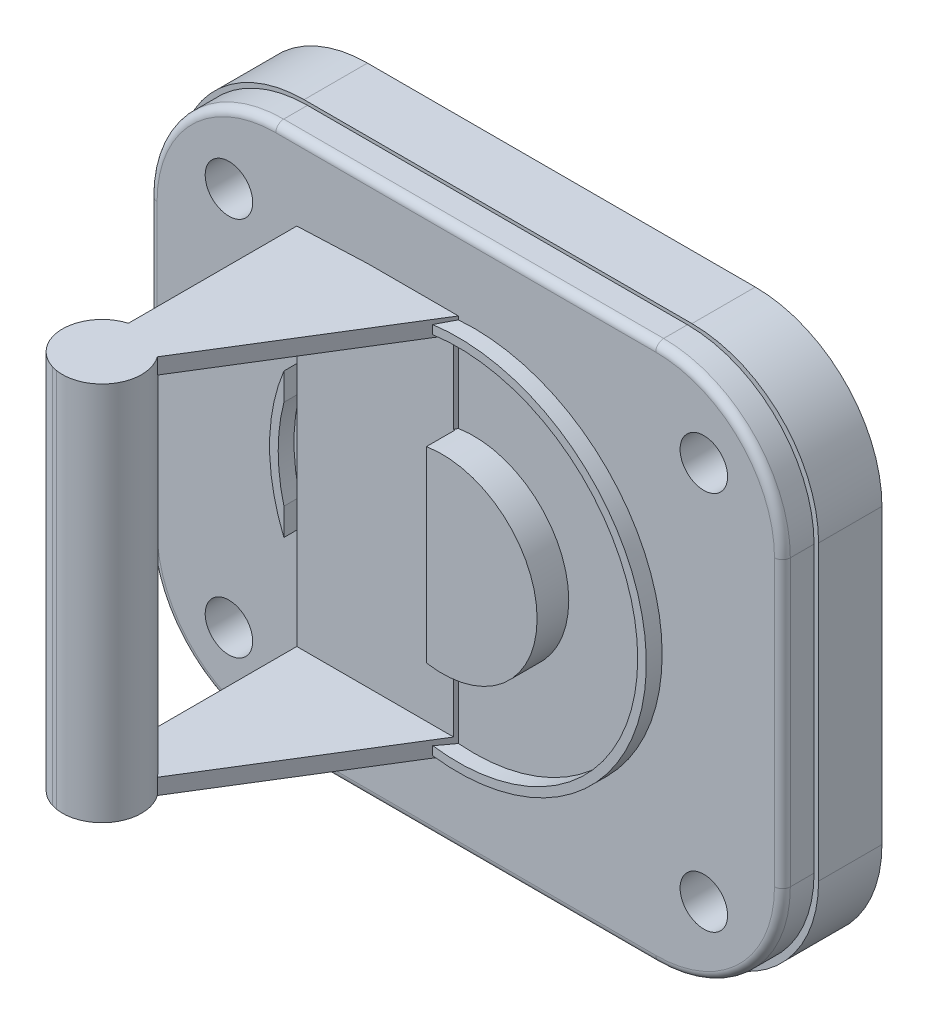
SolidWorks part; units mm, degrees
ref_plane "Front Plane" through (0, 0, 0) normal (0, 0, 1) x (1, 0, 0)
ref_plane "Top Plane" through (0, 0, 0) normal (0, 1, 0) x (1, 0, 0)
ref_plane "Right Plane" through (0, 0, 0) normal (1, 0, 0) x (0, 0, -1)
sketch "Sketch3" plane through (0, 0, 0) normal (0, 0, 1) x (1, 0, 0)
  line L5 (52.0332, 126.753) -> (82.0332, 102.753) construction
  line L6 (52.0332, 102.753) -> (82.0332, 126.753) construction
  line L7 (47.0332, 97.753) -> (87.0332, 97.753)
  line L8 (47.0332, 97.753) -> (47.0332, 131.753)
  line L9 (47.0332, 131.753) -> (87.0332, 131.753)
  line L10 (87.0332, 97.753) -> (87.0332, 131.753)
  line L11 (47.0332, 97.753) -> (87.0332, 131.753) construction
  line L12 (47.0332, 131.753) -> (87.0332, 97.753) construction
  circle A0 centre (82.0332, 126.753) radius 0.25
  circle A1 centre (52.0332, 126.753) radius 0.5
  circle A2 centre (52.0332, 102.753) radius 0.25
  circle A3 centre (82.0332, 102.753) radius 0.5
  circle A4 centre (55.0332, 129.753) radius 0.25 [skipped]
  circle A5 centre (79.0332, 99.753) radius 0.25 [skipped]
  point P0 (67.0332, 114.753)
  point P8 (67.0332, 114.753)
  point P15 (67.0332, 114.753)
  dimension "D3" = 0.5
  dimension "D5" = 1
  dimension "D6" = 1
  dimension "D1" = 30
  dimension "D2" = 24
  dimension "D7" = 40
  dimension "D8" = 34
  dimension "D4" = 4
extrude "Boss-Extrude2" add sketch "Sketch3" along normal blind 2
sketch "Sketch4" plane through (0, 0, 2) normal (0, 0, 1) x (1, 0, 0)
  circle A0 centre (67.5372, 114.9233) radius 6
  dimension "D1" = 12
extrude "Boss-Extrude3" add sketch "Sketch4" along normal blind 2
sketch "Sketch5" plane through (0, 0, 2) normal (0, 0, 1) x (1, 0, 0)
  circle A0 centre (67.5372, 114.9233) radius 11.8998
extrude "Boss-Extrude4" add sketch "Sketch5" along normal blind 1
sketch "Sketch7" plane through (0, 0, 4) normal (0, 0, 1) x (1, 0, 0)
  circle A0 centre (67.5372, 114.9233) radius 6
  circle A1 centre (67.5372, 114.9233) radius 11.8998
  circle A2 centre (67.5372, 114.9233) radius 11.355
  dimension "D1" = 12
extrude "Cut-Extrude1" cut sketch "Sketch7" against normal blind 2 contours A2 A0
ref_plane "Plane1" through (0, 103, 0) normal (0, 1, 0) x (1, 0, 0)
sketch "Sketch10" plane through (0, 103, 0) normal (0, 1, 0) x (1, 0, 0)
  line L0 (66.7201, -1.7479) -> (56.5437, -18.1868)
  line L1 (56.5437, -18.1868) -> (56.5437, -2.1868)
  line L4 (66.7201, -1.7479) -> (56.5437, -2.1868)
  dimension "D1" = 16
extrude "Boss-Extrude5" add sketch "Sketch10" along normal blind 24
sketch "Sketch11" plane through (56.5437, 0, 0) normal (-1, 0, 0) x (0, 0, 1)
  line L0 (18.1868, 115) -> (2.1868, 115) construction
  line L1 (18.1868, 127) -> (18.1868, 103) construction
  line L3 (2.1868, 104) -> (18.1868, 104)
  line L4 (2.1868, 104) -> (2.1868, 126)
  line L5 (2.1868, 126) -> (18.1868, 126)
  line L6 (18.1868, 104) -> (18.1868, 126)
  line L7 (2.1868, 104) -> (18.1868, 126) construction
  line L8 (2.1868, 126) -> (18.1868, 104) construction
  point P4 (10.1868, 115)
  dimension "D1" = 16
  dimension "D2" = 22
  dimension "D3" = 16
extrude "Cut-Extrude2" cut sketch "Sketch11" against normal blind 10
sketch "Sketch12" plane through (0, 103, 0) normal (0, -1, 0) x (1, 0, 0)
  circle A0 centre (57.2684, 15.2134) radius 2.5
  dimension "D1" = 5
extrude "Boss-Extrude6" add sketch "Sketch12" against normal up to surface (24 mm away) up to face at (60.1315, 127, 6.0934)
ref_plane "Plane2" through (0, 106, 0) normal (0, 1, 0) x (1, 0, 0)
sketch "Sketch14" plane through (0, 127, 0) normal (0, 1, 0) x (1, 0, 0)
  line L0 (56.5437, -17.6061) -> (56.5437, -18.1868)
  line L1 (56.5437, -17.6061) -> (56.5437, -18.1868) construction
  line L2 (56.5437, -18.1868) -> (56.8578, -17.6795) construction
  line L3 (56.5437, -18.1868) -> (56.8578, -17.6795)
  line L4 (56.8578, -17.6795) -> (56.5437, -17.6061)
extrude "Cut-Extrude3" cut sketch "Sketch14" against normal blind 26
fillet "Fillet3" radius 8 1 edges at (87.0332, 131.753, 1)
fillet "Fillet4" radius 8 1 edges at (87.0332, 97.753, 1)
fillet "Fillet5" radius 8 1 edges at (47.0332, 131.753, 1)
fillet "Fillet6" radius 8 1 edges at (47.0332, 97.753, 1)
sketch "Sketch16" plane through (0, 0, 0) normal (0, 0, -1) x (-1, 0, 0)
  line L1 (-46.8198, 131.9587) -> (-87.3198, 131.9587)
  line L2 (-46.8198, 131.9587) -> (-46.8198, 97.4587)
  line L3 (-46.8198, 97.4587) -> (-87.3198, 97.4587)
  line L4 (-87.3198, 131.9587) -> (-87.3198, 97.4587)
  line L5 (-46.8198, 131.9587) -> (-87.3198, 97.4587) construction
  line L6 (-46.8198, 97.4587) -> (-87.3198, 131.9587) construction
  point P0 (-67.0698, 114.7087)
  dimension "D1" = 34.5
  dimension "D2" = 40.5
extrude "Boss-Extrude12" add sketch "Sketch16" along normal blind 4
sketch "Sketch21" plane through (0, 0, -4) normal (0, 0, -1) x (-1, 0, 0)
  line L4 (-82.0698, 126.7087) -> (-52.0698, 126.7087) construction
  line L5 (-82.0698, 126.7087) -> (-82.0698, 102.7087) construction
  line L6 (-82.0698, 102.7087) -> (-52.0698, 102.7087) construction
  line L7 (-52.0698, 126.7087) -> (-52.0698, 102.7087) construction
  line L8 (-82.0698, 126.7087) -> (-52.0698, 102.7087) construction
  line L9 (-82.0698, 102.7087) -> (-52.0698, 126.7087) construction
  circle A0 centre (-82.0698, 126.7087) radius 1.5
  circle A1 centre (-52.0698, 126.7087) radius 1.5
  circle A2 centre (-52.0698, 102.7087) radius 1.5
  circle A3 centre (-82.0698, 102.7087) radius 1.5
  point P6 (-67.0698, 114.7087)
  dimension "D3" = 3
  dimension "D4" = 3
  dimension "D5" = 3
  dimension "D6" = 3
  dimension "D1" = 24
  dimension "D2" = 30
extrude "Cut-Extrude10" cut sketch "Sketch21" against normal blind 8
fillet "Fillet13" radius 0.5 8 edges at (49.3763, 100.0961, 2) (47.0332, 114.753, 2) (49.3763, 129.4098, 2) (67.0332, 131.753, 2) (84.69, 129.4098, 2) (87.0332, 114.753, 2) (84.69, 100.0961, 2) (67.0332, 97.753, 2)
fillet "Fillet15" radius 8 4 edges at (87.3198, 97.4587, -2) (87.3198, 131.9587, -2) (46.8198, 131.9587, -2) (46.8198, 97.4587, -2)
